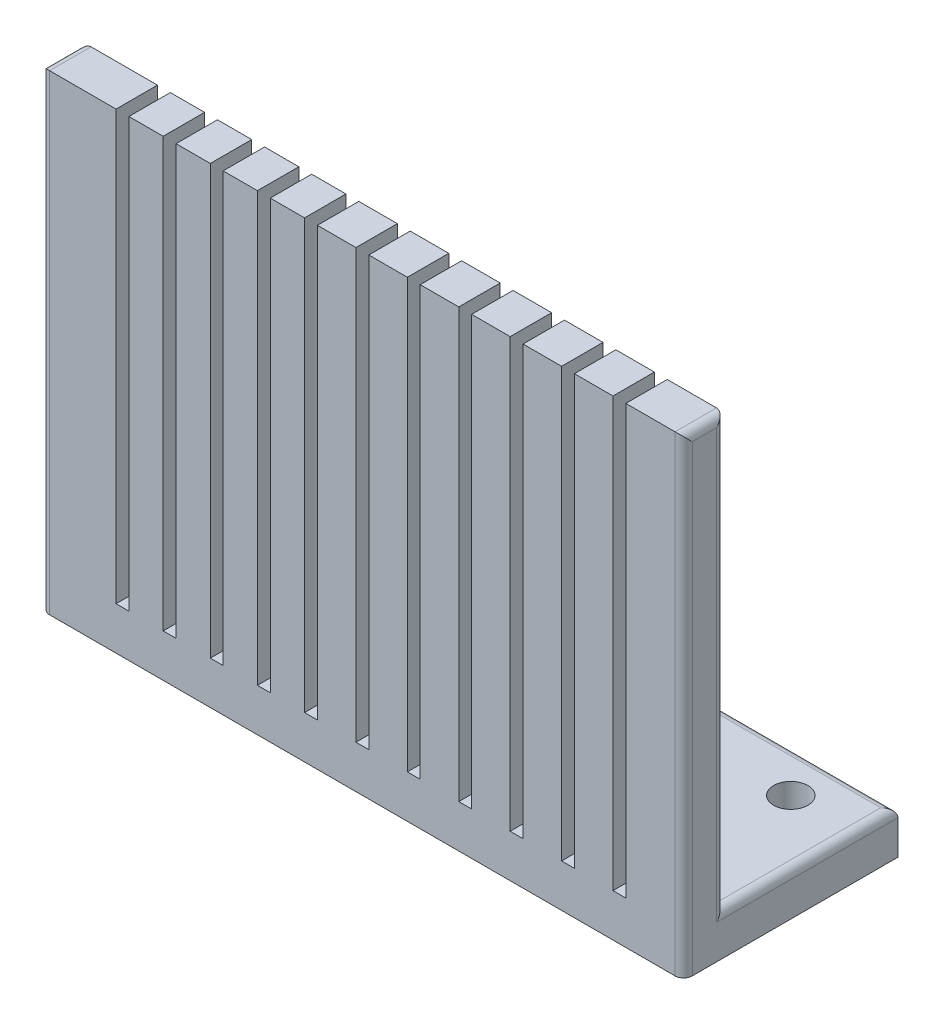
SolidWorks part; units mm, degrees
ref_plane "Front Plane" through (0, 0, 0) normal (0, 0, 1) x (1, 0, 0)
ref_plane "Top Plane" through (0, 0, 0) normal (0, 1, 0) x (1, 0, 0)
ref_plane "Right Plane" through (0, 0, 0) normal (1, 0, 0) x (0, 0, -1)
sketch "Sketch1" plane through (0, 0, 0) normal (0, 1, 0) x (1, 0, 0)
  line L0 (0, -25) -> (0, 25) construction
  line L1 (75, -25) -> (-75, -25)
  line L2 (75, -25) -> (75, 25)
  line L3 (75, 25) -> (-75, 25)
  line L4 (-75, -25) -> (-75, 25)
  line L5 (75, -25) -> (-75, 25) construction
  line L6 (75, 25) -> (-75, -25) construction
  circle A0 centre (60, 15) radius 4
  circle A1 centre (-60, 15) radius 4
  point P0 (0, 0)
  dimension "D1" = 50
  dimension "D2" = 150
  dimension "D3" = 120
  dimension "D4" = 10
extrude "Boss-Extrude1" add sketch "Sketch1" along normal blind 10
sketch "Sketch2" plane through (0, 10, 0) normal (0, 1, 0) x (1, 0, 0)
  line L0 (-75, -25) -> (75, -25) construction
  line L1 (-75, -25) -> (75, -25)
  line L2 (-75, -25) -> (-75, -15.3323)
  line L3 (-75, -15.3323) -> (75, -15.3323)
  line L4 (75, -25) -> (75, -15.3323)
  line L5 (0, 0) -> (0, -25) construction
  dimension "D1" = 150
extrude "Boss-Extrude2" add sketch "Sketch2" along normal blind 100
sketch "Sketch3" plane through (0, 0, 15.3323) normal (0, 0, -1) x (-1, 0, 0)
  line L0 (-13.5, 110) -> (-13.5, 10)
  line L1 (-75, 110) -> (75, 110) construction
  line L2 (-75, 10) -> (75, 10) construction
  line L3 (-10.5, 110) -> (-10.5, 10)
  line L4 (-1.5, 110) -> (-1.5, 10)
  line L5 (-75, 10) -> (75, 10) construction
  line L6 (1.5, 110) -> (1.5, 10)
  line L7 (10.5, 110) -> (10.5, 10)
  line L8 (13.5, 110) -> (13.5, 10)
  line L9 (0, 110) -> (0, 10) construction
  line L10 (-13.5, 110) -> (-10.5, 110)
  line L11 (-1.5, 110) -> (1.5, 110)
  line L12 (10.5, 110) -> (13.5, 110)
  line L13 (13.5, 10) -> (10.5, 10)
  line L14 (1.5, 10) -> (-1.5, 10)
  line L15 (-10.5, 10) -> (-13.5, 10)
  line L16 (24.5, 10) -> (21.5, 10)
  line L17 (21.5, 110) -> (21.5, 10)
  line L18 (21.5, 110) -> (24.5, 110)
  line L19 (24.5, 110) -> (24.5, 10)
  line L20 (35.5, 10) -> (32.5, 10)
  line L21 (32.5, 110) -> (32.5, 10)
  line L22 (32.5, 110) -> (35.5, 110)
  line L23 (35.5, 110) -> (35.5, 10)
  line L24 (46.5, 10) -> (43.5, 10)
  line L25 (43.5, 110) -> (43.5, 10)
  line L26 (43.5, 110) -> (46.5, 110)
  line L27 (46.5, 110) -> (46.5, 10)
  line L28 (57.5, 10) -> (54.5, 10)
  line L29 (54.5, 110) -> (54.5, 10)
  line L30 (54.5, 110) -> (57.5, 110)
  line L31 (57.5, 110) -> (57.5, 10)
  line L36 (-22.5, 10) -> (-25.5, 10)
  line L37 (-25.5, 110) -> (-25.5, 10)
  line L38 (-25.5, 110) -> (-22.5, 110)
  line L39 (-22.5, 110) -> (-22.5, 10)
  line L40 (-34.5, 10) -> (-37.5, 10)
  line L41 (-37.5, 110) -> (-37.5, 10)
  line L42 (-37.5, 110) -> (-34.5, 110)
  line L43 (-34.5, 110) -> (-34.5, 10)
  line L44 (-46.5, 10) -> (-49.5, 10)
  line L45 (-49.5, 110) -> (-49.5, 10)
  line L46 (-49.5, 110) -> (-46.5, 110)
  line L47 (-46.5, 110) -> (-46.5, 10)
  line L48 (-58.5, 10) -> (-61.5, 10)
  line L49 (-61.5, 110) -> (-61.5, 10)
  line L50 (-61.5, 110) -> (-58.5, 110)
  line L51 (-58.5, 110) -> (-58.5, 10)
  line L56 (-70.5, 110) -> (-70.5, 10) [skipped]
  line L57 (-70.5, 10) -> (-73.5, 10) [skipped]
  line L58 (-73.5, 110) -> (-73.5, 10) [skipped]
  line L59 (-73.5, 110) -> (-70.5, 110) [skipped]
  line L60 (65.5, 110) -> (65.5, 10) [skipped]
  line L61 (68.5, 10) -> (65.5, 10) [skipped]
  line L62 (65.5, 110) -> (68.5, 110) [skipped]
  line L63 (68.5, 110) -> (68.5, 10) [skipped]
  dimension "D1" = 3
  dimension "D2" = 3
  dimension "D3" = 9
  dimension "D6" = 8
  dimension "D7" = 9
  dimension "D4" = 6
  dimension "D5" = 6
extrude "Cut-Extrude1" cut sketch "Sketch3" against normal blind 100
fillet "Fillet1" radius 2 9 edges at (0, 10, -25) (75, 10, -4.8338) (-75, 60, 15.3323) (75, 60, 15.3323) (-75, 110, 20.1662) (75, 110, 20.1662) (-75, 10, -4.8338) (75, 55, 25) (-75, 55, 25)
